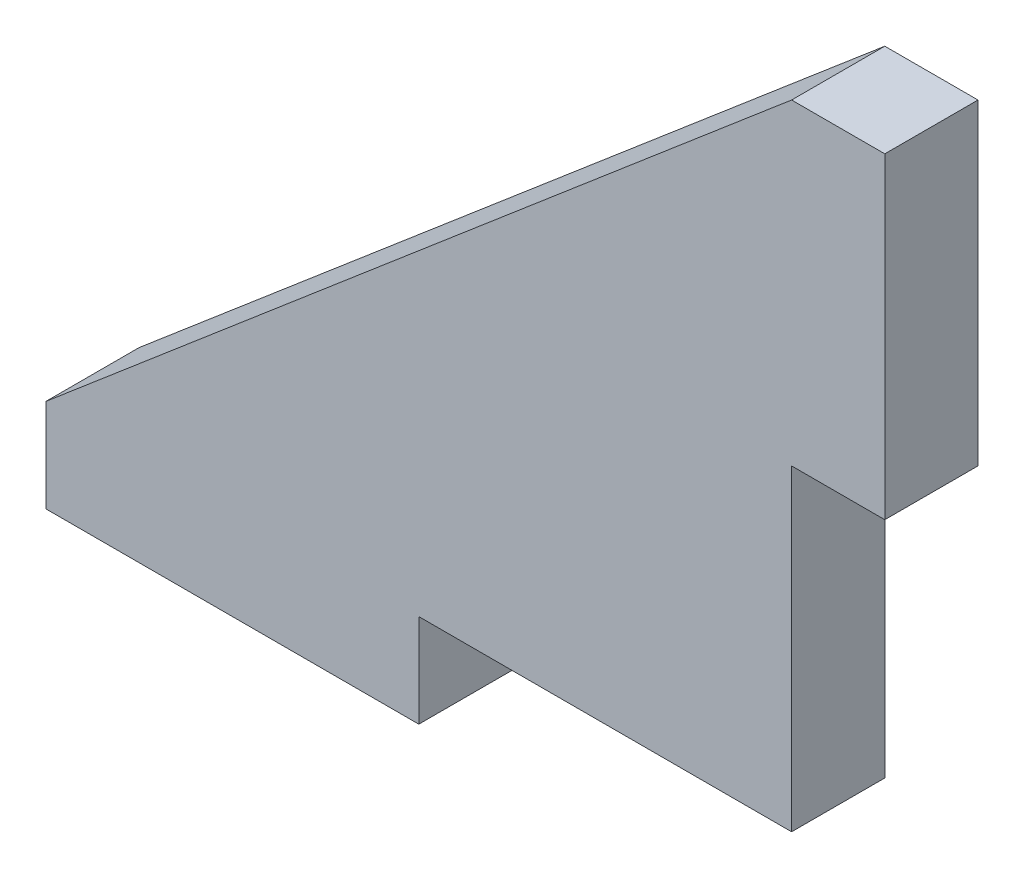
SolidWorks part; units mm, degrees
ref_plane "Alzado" through (0, 0, 0) normal (0, 0, 1) x (1, 0, 0)
ref_plane "Planta" through (0, 0, 0) normal (0, 1, 0) x (1, 0, 0)
ref_plane "Vista lateral" through (0, 0, 0) normal (1, 0, 0) x (0, 0, -1)
sketch "Croquis1" plane through (0, 0, 0) normal (0, 0, 1) x (1, 0, 0)
  line L0 (0, 0) -> (40, 34)
  line L1 (40, 34) -> (40, 0)
  line L2 (40, 0) -> (0, 0)
  line L4 (40, 34) -> (45, 34)
  line L5 (40, 34) -> (40, 17)
  line L6 (40, 17) -> (45, 17)
  line L7 (45, 34) -> (45, 17)
  line L8 (0, 0) -> (20, 0)
  line L9 (0, 0) -> (0, -5)
  line L10 (0, -5) -> (20, -5)
  line L11 (20, 0) -> (20, -5)
  point P7 (40, 17)
  point P12 (20, 0)
  dimension "D1" = 40
  dimension "D2" = 34
  dimension "D3" = 5
  dimension "D4" = 5
extrude "Saliente-Extruir1" add sketch "Croquis1" along normal blind 5 contours L7 L4 L1 L6 | L2 L1 L0 | L11 L2 L9 L10
